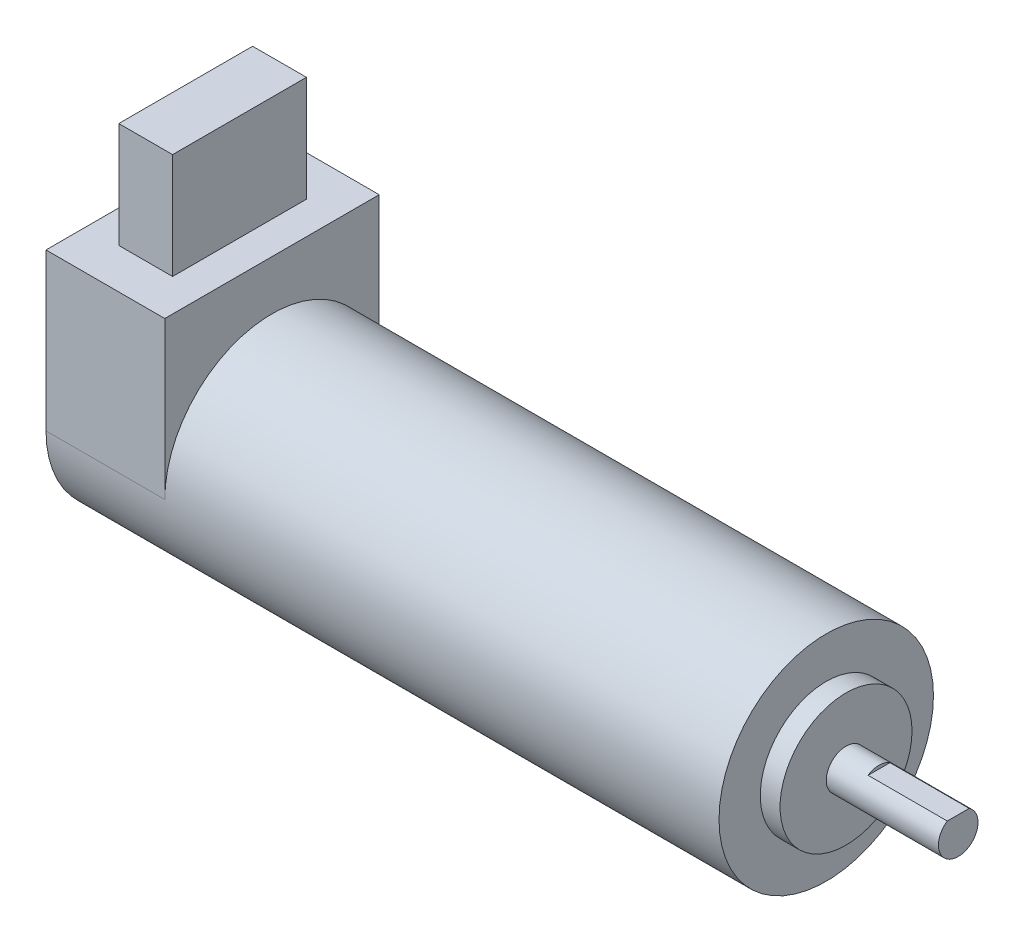
SolidWorks part; units mm, degrees
ref_plane "Front Plane" through (0, 0, 0) normal (0, 0, 1) x (1, 0, 0)
ref_plane "Top Plane" through (0, 0, 0) normal (0, 1, 0) x (1, 0, 0)
ref_plane "Right Plane" through (0, 0, 0) normal (1, 0, 0) x (0, 0, -1)
sketch "Sketch1" plane through (0, 0, 0) normal (1, 0, 0) x (0, 0, -1)
  circle A0 centre (0, 0) radius 16.25
  dimension "D1" = 32.5
extrude "Boss-Extrude1" add sketch "Sketch1" along normal blind 84
sketch "Sketch2" plane through (84, 0, 0) normal (1, 0, 0) x (0, 0, -1)
  circle A0 centre (0, 0) radius 10
  dimension "D1" = 20
extrude "Boss-Extrude2" add sketch "Sketch2" along normal blind 3
sketch "Sketch3" plane through (87, 0, 0) normal (1, 0, 0) x (0, 0, -1)
  circle A0 centre (0, 0) radius 3
  dimension "D1" = 6
extrude "Boss-Extrude3" add sketch "Sketch3" along normal blind 17
sketch "Sketch4" plane through (104, 0, 0) normal (1, 0, 0) x (0, 0, -1)
  line L0 (-1.6583, 2.5) -> (1.6583, 2.5)
  circle A0 centre (0, 0) radius 3 construction
  circle A1 centre (0, 0) radius 3 construction
  circle A2 centre (0, 0) radius 3
  circle M3 centre (0, 0) radius 3
  dimension "D1" = 5.5
extrude "Cut-Extrude1" cut sketch "Sketch4" against normal blind 12 contours L0 M3
sketch "Sketch5" plane through (0, 0, 0) normal (-1, 0, 0) x (0, 0, 1)
  line L0 (-16.25, 0) -> (-16.25, 23.75)
  line L1 (-16.25, 23.75) -> (16.25, 23.75)
  line L2 (16.25, 23.75) -> (16.25, 0)
  circle A0 centre (0, 0) radius 16.25 construction
  circle A1 centre (0, 0) radius 16.25
  circle M2 centre (0, 0) radius 16.25
  dimension "D1" = 40
extrude "Boss-Extrude4" add sketch "Sketch5" along normal blind 18 contours M2 | L2 L1 L0 M2
sketch "Sketch6" plane through (0, 23.75, 0) normal (0, 1, 0) x (1, 0, 0)
  line L0 (-9, -16.25) -> (-9, 16.25) construction
  line L1 (-18, -16.25) -> (0, -16.25) construction
  line L2 (-18, 16.25) -> (0, 16.25) construction
  line L4 (-13.0774, -10.144) -> (-4.9226, -10.144)
  line L5 (-13.0774, -10.144) -> (-13.0774, 10.144)
  line L6 (-13.0774, 10.144) -> (-4.9226, 10.144)
  line L7 (-4.9226, -10.144) -> (-4.9226, 10.144)
  line L8 (-13.0774, -10.144) -> (-4.9226, 10.144) construction
  line L9 (-13.0774, 10.144) -> (-4.9226, -10.144) construction
  point P6 (-9, 0)
extrude "Boss-Extrude5" add sketch "Sketch6" along normal blind 16
